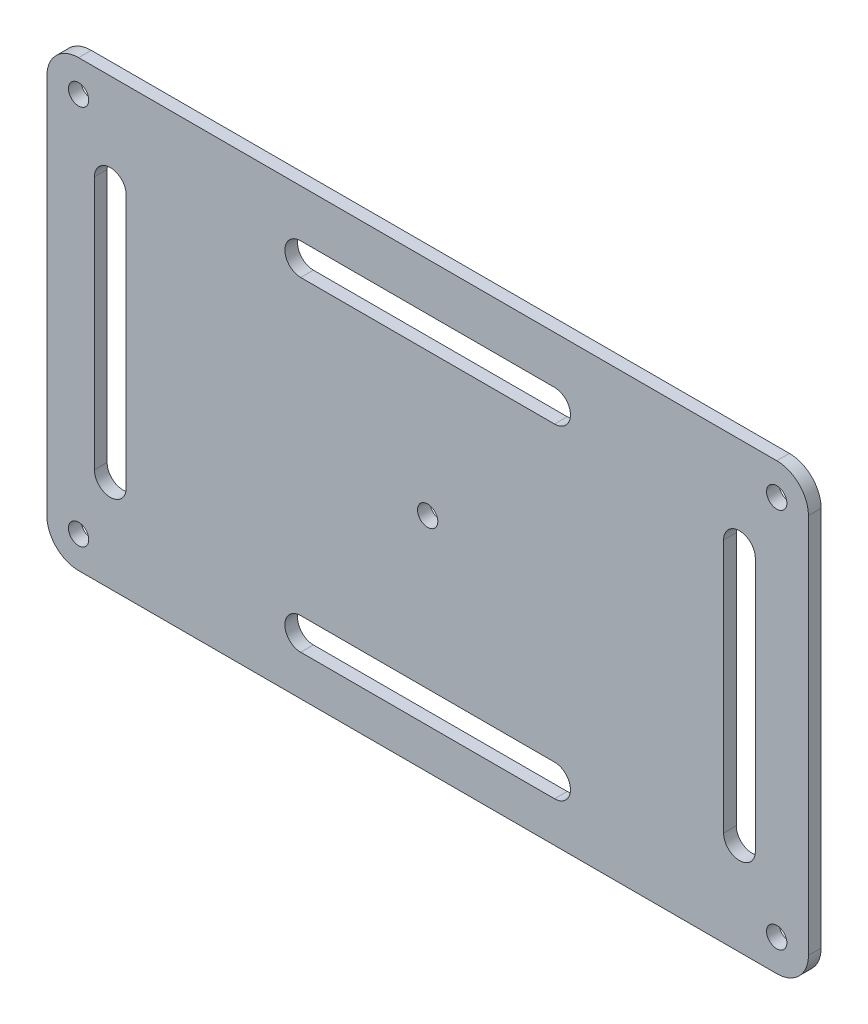
SolidWorks part; units mm, degrees
ref_plane "Front Plane" through (0, 0, 0) normal (0, 0, 1) x (1, 0, 0)
ref_plane "Top Plane" through (0, 0, 0) normal (0, 1, 0) x (1, 0, 0)
ref_plane "Right Plane" through (0, 0, 0) normal (1, 0, 0) x (0, 0, -1)
sketch "Sketch1" plane through (0, 0, 0) normal (0, 0, 1) x (1, 0, 0)
  line L0 (-53.4, 30) -> (-55, 30)
  line L1 (55, 35) -> (-55, 35)
  line L2 (60, 30) -> (60, -30)
  line L3 (55, -35) -> (-55, -35)
  line L4 (-60, 30) -> (-60, -30)
  line L5 (0, -35) -> (0, 35) construction
  line L6 (60, 0) -> (-60, 0) construction
  line L7 (55, 30) -> (53.4, 30)
  line L8 (55, 30) -> (55, 28.4)
  line L9 (55, -30) -> (53.4, -30)
  line L10 (-55, 30) -> (-55, 28.4)
  line L11 (0, -30) -> (0, 30) construction
  line L12 (55, 0) -> (-55, 0) construction
  line L13 (-55, -28.4) -> (-55, -30)
  line L14 (55, -28.4) -> (55, -30)
  line L15 (-53.4, -30) -> (-55, -30)
  line L16 (-60, 0) -> (-50, 0) construction
  line L17 (-20, 25) -> (20, 25) construction
  line L18 (0, 35) -> (0, 20) construction
  line L19 (-20, 27.5) -> (20, 27.5)
  line L20 (-20, 22.5) -> (20, 22.5)
  line L21 (-50, 20) -> (-50, -20) construction
  line L22 (-47.5, 20) -> (-47.5, -20)
  line L23 (-52.5, 20) -> (-52.5, -20)
  line L24 (-20, -26.1362) -> (20, -26.1362) construction
  line L25 (-20, -23.6362) -> (20, -23.6362)
  line L26 (-20, -28.6362) -> (20, -28.6362)
  line L27 (49.1289, 20) -> (49.1289, -20) construction
  line L28 (51.6289, 20) -> (51.6289, -20)
  line L29 (46.6289, 20) -> (46.6289, -20)
  circle A0 centre (-55, 30) radius 1.6
  circle A1 centre (-55, -30) radius 1.6
  circle A2 centre (55, -30) radius 1.6
  circle A3 centre (55, 30) radius 1.6
  circle A4 centre (0, 0) radius 1.6
  arc A5 (-20, 27.5) -> (-20, 22.5) centre (-20, 25) ccw
  arc A6 (20, 22.5) -> (20, 27.5) centre (20, 25) ccw
  arc A7 (-47.5, 20) -> (-52.5, 20) centre (-50, 20) ccw
  arc A8 (-52.5, -20) -> (-47.5, -20) centre (-50, -20) ccw
  arc A9 (-20, -23.6362) -> (-20, -28.6362) centre (-20, -26.1362) ccw
  arc A10 (20, -28.6362) -> (20, -23.6362) centre (20, -26.1362) ccw
  arc A11 (51.6289, 20) -> (46.6289, 20) centre (49.1289, 20) ccw
  arc A12 (46.6289, -20) -> (51.6289, -20) centre (49.1289, -20) ccw
  arc A13 (-60, 30) -> (-55, 35) centre (-55, 30) cw
  arc A14 (-60, -30) -> (-55, -35) centre (-55, -30) ccw
  arc A15 (55, -35) -> (60, -30) centre (55, -30) ccw
  arc A16 (60, 30) -> (55, 35) centre (55, 30) ccw
  point P0 (0, 0)
  point P4 (0, 0)
  point P24 (0, 25)
  point P33 (-50, 0)
  point P40 (0, -26.1362)
  point P47 (49.1289, 0)
  point P54 (-60, 35)
  point P58 (-60, -35)
  point P63 (60, 35)
  dimension "D5" = 10
  dimension "D7" = 5
  dimension "D8" = 5
  dimension "D9" = 5
  dimension "D10" = 5
  dimension "D1" = 120
  dimension "D2" = 70
  dimension "D3" = 110
  dimension "D4" = 60
  dimension "D6" = 10
extrude "Boss-Extrude1" add sketch "Sketch1" along normal blind 2 contours L1 L4 L3 L2 A12 L29 A11 L28 A10 L26 A9 L25 A8 L23 A7 L22 A6 L20 A5 L19 A4 A3 A2 A1 A0
